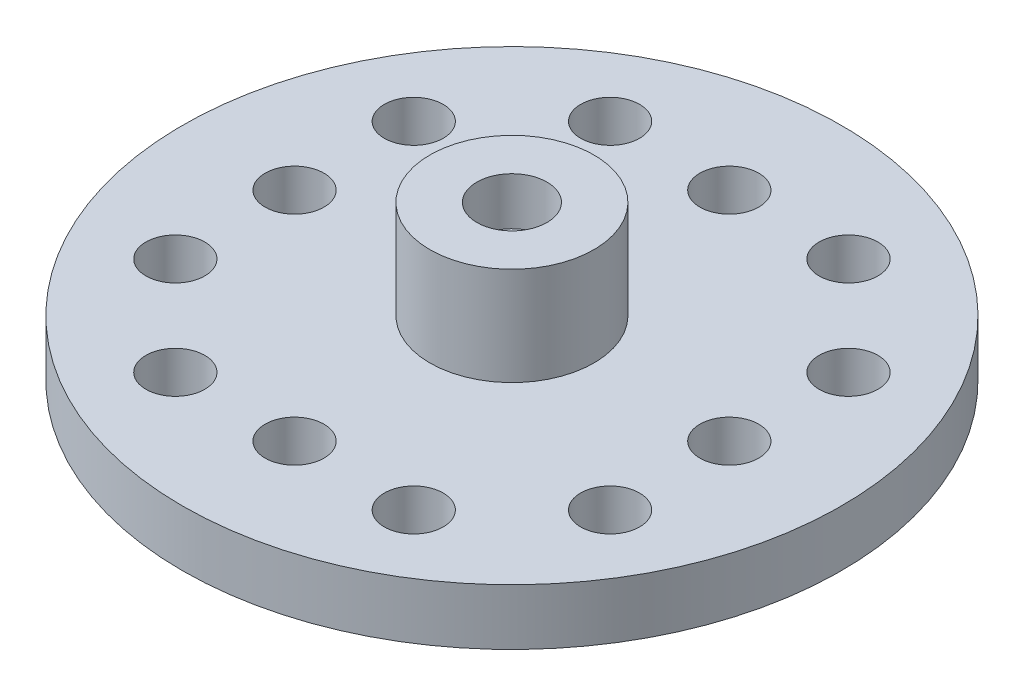
SolidWorks part; units mm, degrees
ref_plane "Front Plane" through (0, 0, 0) normal (0, 0, 1) x (1, 0, 0)
ref_plane "Top Plane" through (0, 0, 0) normal (0, 1, 0) x (1, 0, 0)
ref_plane "Right Plane" through (0, 0, 0) normal (1, 0, 0) x (0, 0, -1)
sketch "草圖1" plane through (0, 0, 0) normal (0, 1, 0) x (1, 0, 0)
  circle A0 centre (0, 0) radius 23.5
  dimension "D1" = 47
extrude "填料-伸長1" add sketch "草圖1" along normal blind 4
sketch "草圖2" plane through (0, 4, 0) normal (0, 1, 0) x (1, 0, 0)
  circle A0 centre (0, 0) radius 5.85
  dimension "D1" = 11.7
extrude "填料-伸長2" add sketch "草圖2" along normal blind 7
sketch "草圖3" plane through (0, 11, 0) normal (0, 1, 0) x (1, 0, 0)
  circle A0 centre (0, 0) radius 2.5
  dimension "D1" = 5
extrude "除料-伸長1" cut sketch "草圖3" against normal blind 3.4
sketch "草圖4" plane through (0, 4, 0) normal (0, 1, 0) x (1, 0, 0)
  line L0 (-15.5, -8.5) -> (-15.5, 8.5) construction
  line L1 (-15.5, 0) -> (0, 0) construction
  circle A0 centre (-15.5, 0) radius 2.1
  circle A1 centre (-15.5, 8.5) radius 2.1
  circle A2 centre (-15.5, -8.5) radius 2.1
  point P3 (-15.5, 0)
  dimension "D1" = 4.2
  dimension "D2" = 8.5
  dimension "D3" = 15.5
extrude "除料-伸長2" cut sketch "草圖4" against normal through all
pattern_circular "環狀複製排列1" count 4 over 360 about axis through (0, 0, 0) along (0, 1, 0) of "除料-伸長2"
sketch "草圖5" plane through (0, 7.6, 0) normal (0, 1, 0) x (1, 0, 0)
  circle A0 centre (0, 0) radius 2
  dimension "D1" = 4
extrude "除料-伸長3" cut sketch "草圖5" against normal through all
